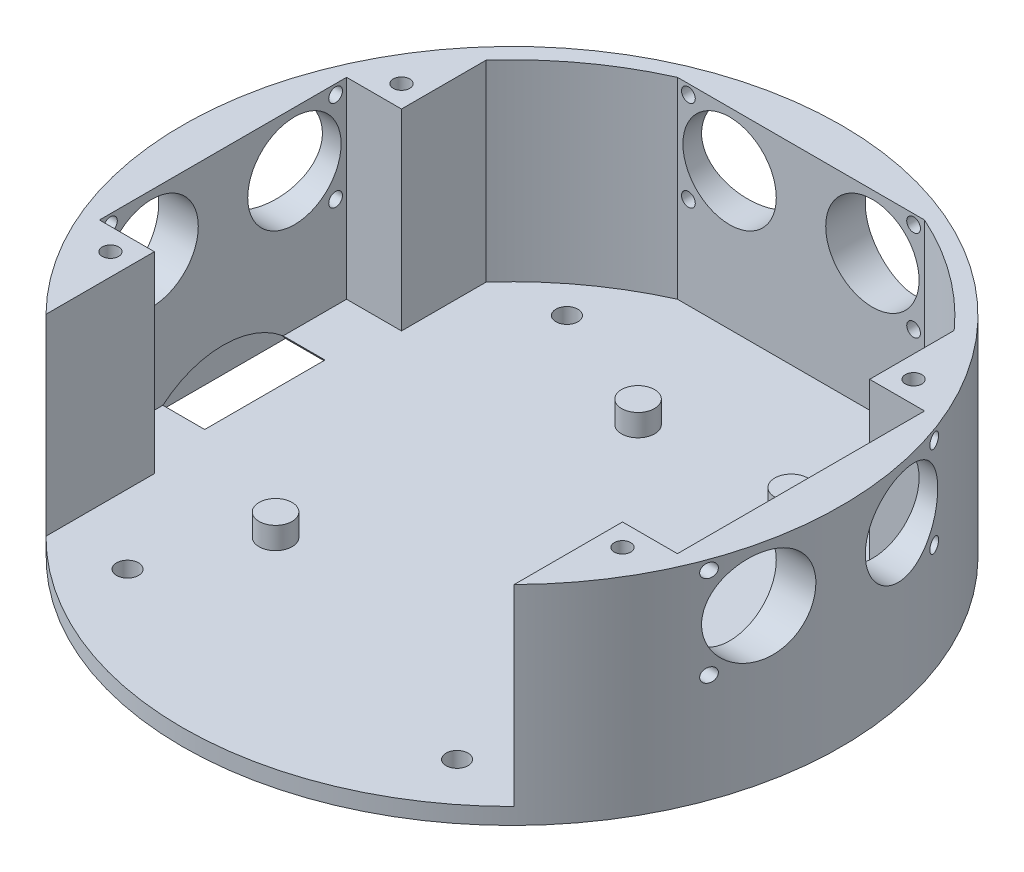
SolidWorks part; units mm, degrees
ref_plane "Front Plane" through (0, 0, 0) normal (0, 0, 1) x (1, 0, 0)
ref_plane "Top Plane" through (0, 0, 0) normal (0, 1, 0) x (1, 0, 0)
ref_plane "Right Plane" through (0, 0, 0) normal (1, 0, 0) x (0, 0, -1)
sketch "Sketch1" plane through (0, 0, 0) normal (0, 1, 0) x (1, 0, 0)
  circle A0 centre (0, 0) radius 60
  dimension "D1" = 120
extrude "Boss-Extrude1" add sketch "Sketch1" along normal blind 3
sketch "Sketch2" plane through (0, 3, 0) normal (0, 1, 0) x (1, 0, 0)
  line L0 (-26.55, 34.3) -> (26.55, -34.3) construction
  line L1 (-26.55, 34.3) -> (26.55, 34.3) construction
  line L2 (-26.55, 34.3) -> (-26.55, -34.3) construction
  line L3 (-26.55, -34.3) -> (26.55, -34.3) construction
  line L4 (26.55, 34.3) -> (26.55, -34.3) construction
  circle A0 centre (-6.35, 29.3) radius 3
  circle A1 centre (21.55, 29.3) radius 3
  circle A2 centre (-21.55, -21.5) radius 3
  point P6 (0, 0)
  dimension "D1" = 6
  dimension "D2" = 27.9
  dimension "D3" = 15.2
  dimension "D4" = 50.8
  dimension "D5" = 5
  dimension "D6" = 5
  dimension "D7" = 5
  dimension "D8" = 68.6
extrude "Boss-Extrude2" add sketch "Sketch2" along normal blind 4
sketch "Sketch3" plane through (0, 3, 0) normal (0, 1, 0) x (1, 0, 0)
  line L1 (-22.5, 55.6215) -> (22.5, 55.6215) construction
  line L2 (-22.5, 55.6215) -> (-22.5, 52.6215)
  line L3 (-22.5, 52.6215) -> (22.5, 52.6215)
  line L4 (22.5, 55.6215) -> (22.5, 52.6215)
  circle A0 centre (0, 0) radius 60 construction
  arc A1 (-22.5, 55.6215) -> (22.5, 55.6215) centre (0, 0) cw
  point P4 (0, 52.6215)
  dimension "D3" = 60
  dimension "D1" = 45
  dimension "D2" = 3
extrude "Boss-Extrude3" add sketch "Sketch3" along normal blind 35
sketch "Sketch4" plane through (0, 0, -52.6215) normal (0, 0, 1) x (1, 0, 0)
  line L0 (-13, 28) -> (13, 28) construction
  line L1 (-22.5, 38) -> (22.5, 38) construction
  line L2 (-22.5, 18) -> (22.5, 18) construction
  line L3 (-22.5, 18) -> (-22.5, 38) construction
  line L4 (-22.5, 38) -> (22.5, 38) construction
  line L5 (22.5, 18) -> (22.5, 38) construction
  line L6 (-22.5, 18) -> (22.5, 38) construction
  line L7 (-22.5, 38) -> (22.5, 18) construction
  line L8 (-20.5, 19.75) -> (20.5, 19.75) construction
  line L9 (20.5, 19.75) -> (20.5, 36.25) construction
  circle A0 centre (-13, 28) radius 8.5
  circle A1 centre (13, 28) radius 8.5
  circle A2 centre (-20.5, 19.75) radius 1.25
  circle A3 centre (20.5, 36.25) radius 1.25
  circle A4 centre (-20.5, 36.25) radius 1.25
  circle A5 centre (20.5, 19.75) radius 1.25
  point P4 (0, 28)
  point P5 (0, 28)
  point P17 (0, 19.75)
  point P19 (20.5, 28)
  dimension "D2" = 17
  dimension "D7" = 2.5
  dimension "D8" = 2.5
  dimension "D9" = 2.5
  dimension "D1" = 26
  dimension "D3" = 45
  dimension "D4" = 20
  dimension "D5" = 16.5
  dimension "D6" = 41
extrude "Cut-Extrude1" cut sketch "Sketch4" against normal through all both and the other way through all
pattern_circular "CirPattern1" count 2 every 90 about axis through (0, 0, 0) along (0, 1, 0) of "Boss-Extrude3", "Cut-Extrude1"
sketch "Sketch5" plane through (0, 3, 0) normal (0, 1, 0) x (1, 0, 0)
  line L1 (-30, -40) -> (30, -40) construction
  line L2 (-30, -40) -> (-30, 40) construction
  line L3 (-30, 40) -> (30, 40) construction
  line L4 (30, -40) -> (30, 40) construction
  line L5 (-30, -40) -> (30, 40) construction
  line L6 (-30, 40) -> (30, -40) construction
  circle A0 centre (-30, 40) radius 2
  circle A1 centre (30, 40) radius 2
  circle A2 centre (30, -40) radius 2
  circle A3 centre (-30, -40) radius 2
  point P0 (0, 0)
  dimension "D3" = 4
  dimension "D1" = 60
  dimension "D2" = 80
extrude "Cut-Extrude2" cut sketch "Sketch5" against normal through all both and the other way through all
ref_plane "Plane1" through (-55, 0, 0) normal (-1, 0, 0) x (0, 0, 1)
sketch "Sketch7" plane through (-55, 0, 0) normal (-1, 0, 0) x (0, 0, 1)
  line L0 (-6.5, -5) -> (-6.5, -15) construction
  line L1 (-6.5, -5) -> (-6.5, -15) construction
  line L2 (-6.5, -5) -> (6.5, -5) construction
  line L3 (-6.5, -15) -> (6.5, -5) construction
  circle A0 centre (0, -10) radius 17
  dimension "D1" = 34
extrude "Cut-Extrude3" cut sketch "Sketch7" against normal blind 10
mirror "Mirror1" about plane through (0, 0, 0) normal (1, 0, 0) of "Cut-Extrude3"
sketch "Sketch8" plane through (0, 3, 0) normal (0, 1, 0) x (1, 0, 0)
  line L1 (-55.6215, 22.5) -> (-52.6215, 22.5)
  line L2 (-52.6215, 22.5) -> (-42.6215, 22.5)
  line L3 (-42.6215, 22.5) -> (-42.6215, 37.8945)
  line L4 (55.6215, 22.5) -> (52.6215, 22.5)
  line L5 (52.6215, 22.5) -> (42.6215, 22.5)
  line L6 (42.6215, 22.5) -> (42.6215, 37.8945)
  line L7 (-22.5, 52.6215) -> (-22.5, 55.6215)
  line L8 (22.5, 55.6215) -> (22.5, 52.6215)
  line L9 (-55.6215, -22.5) -> (-42.6215, -22.5)
  line L10 (-42.6215, -22.5) -> (-42.6215, -42.2304)
  line L11 (55.6215, -22.5) -> (42.6215, -22.5)
  line L12 (42.6215, -22.5) -> (42.6215, -42.2304)
  arc A0 (-55.6215, 22.5) -> (-22.5, 55.6215) centre (0, 0) cw
  arc A1 (-52.6215, 22.5) -> (-22.5, 52.6215) centre (2.1025, -2.1025) cw construction
  arc A2 (22.5, 52.6215) -> (52.6215, 22.5) centre (-2.1025, -2.1025) cw construction
  arc A3 (22.5, 55.6215) -> (55.6215, 22.5) centre (0, 0) cw
  arc A4 (-42.6215, 37.8945) -> (-22.5, 52.6215) centre (2.1025, -2.1025) cw
  arc A5 (22.5, 52.6215) -> (42.6215, 37.8945) centre (-2.1025, -2.1025) cw
  arc A6 (-55.6215, -22.5) -> (55.6215, -22.5) centre (0, 0) ccw construction
  arc A7 (-55.6215, -22.5) -> (-42.6215, -42.2304) centre (0, 0) ccw
  arc A8 (42.6215, -42.2304) -> (55.6215, -22.5) centre (0, 0) ccw
  dimension "D1" = 60
  dimension "D2" = 60
  dimension "D3" = 60
  dimension "D4" = 60
  dimension "D7" = 60
  dimension "D8" = 60
  dimension "D5" = 10
  dimension "D6" = 10
  dimension "D9" = 13
  dimension "D10" = 13
extrude "Boss-Extrude4" add sketch "Sketch8" along normal blind 35
sketch "Sketch9" plane through (0, 38, 0) normal (0, 1, 0) x (1, 0, 0)
  line L11 (-42.6215, -42.2304) -> (-42.6215, -22.5)
  line L12 (-42.6215, -22.5) -> (-52.6215, -22.5)
  line L13 (-52.6215, -22.5) -> (-52.6215, 22.5)
  line L14 (-52.6215, 22.5) -> (-42.6215, 22.5)
  line L15 (-42.6215, 22.5) -> (-42.6215, 37.8945)
  line L16 (-22.5, 52.6215) -> (22.5, 52.6215)
  line L17 (42.6215, 37.8945) -> (42.6215, 22.5)
  line L18 (42.6215, 22.5) -> (52.6215, 22.5)
  line L19 (52.6215, 22.5) -> (52.6215, -22.5)
  line L20 (52.6215, -22.5) -> (42.6215, -22.5)
  line L21 (42.6215, -22.5) -> (42.6215, -42.2304)
  line L22 (-42.6215, -42.2304) -> (-42.6215, -22.5) construction
  line L23 (-42.6215, -22.5) -> (-52.6215, -22.5) construction
  line L24 (-52.6215, -22.5) -> (-52.6215, 22.5) construction
  line L25 (-52.6215, 22.5) -> (-42.6215, 22.5) construction
  line L26 (-42.6215, 22.5) -> (-42.6215, 37.8945) construction
  line L27 (-22.5, 52.6215) -> (22.5, 52.6215) construction
  line L28 (42.6215, 37.8945) -> (42.6215, 22.5) construction
  line L29 (42.6215, 22.5) -> (52.6215, 22.5) construction
  line L30 (52.6215, 22.5) -> (52.6215, -22.5) construction
  line L31 (52.6215, -22.5) -> (42.6215, -22.5) construction
  line L32 (42.6215, -22.5) -> (42.6215, -42.2304) construction
  circle A0 centre (-46.6215, 26.5) radius 1.5
  circle A1 centre (-46.6215, -26.5) radius 1.5
  circle A2 centre (46.6215, -26.5) radius 1.5
  arc A3 (42.6215, -42.2304) -> (-42.6215, -42.2304) centre (0, 0) ccw
  arc A4 (-22.5, 52.6215) -> (-42.6215, 37.8945) centre (2.1025, -2.1025) ccw
  arc A5 (42.6215, 37.8945) -> (22.5, 52.6215) centre (-2.1025, -2.1025) ccw
  arc A6 (42.6215, -42.2304) -> (-42.6215, -42.2304) centre (0, 0) ccw construction
  arc A7 (-22.5, 52.6215) -> (-42.6215, 37.8945) centre (2.1025, -2.1025) ccw construction
  arc A8 (42.6215, 37.8945) -> (22.5, 52.6215) centre (-2.1025, -2.1025) ccw construction
  circle A9 centre (46.6215, 26.5) radius 1.5
  dimension "D2" = 3
  dimension "D3" = 4
  dimension "D4" = 4
  dimension "D5" = 4
  dimension "D6" = 4
  dimension "D1" = 0
extrude "Cut-Extrude4" cut sketch "Sketch9" against normal blind 35
